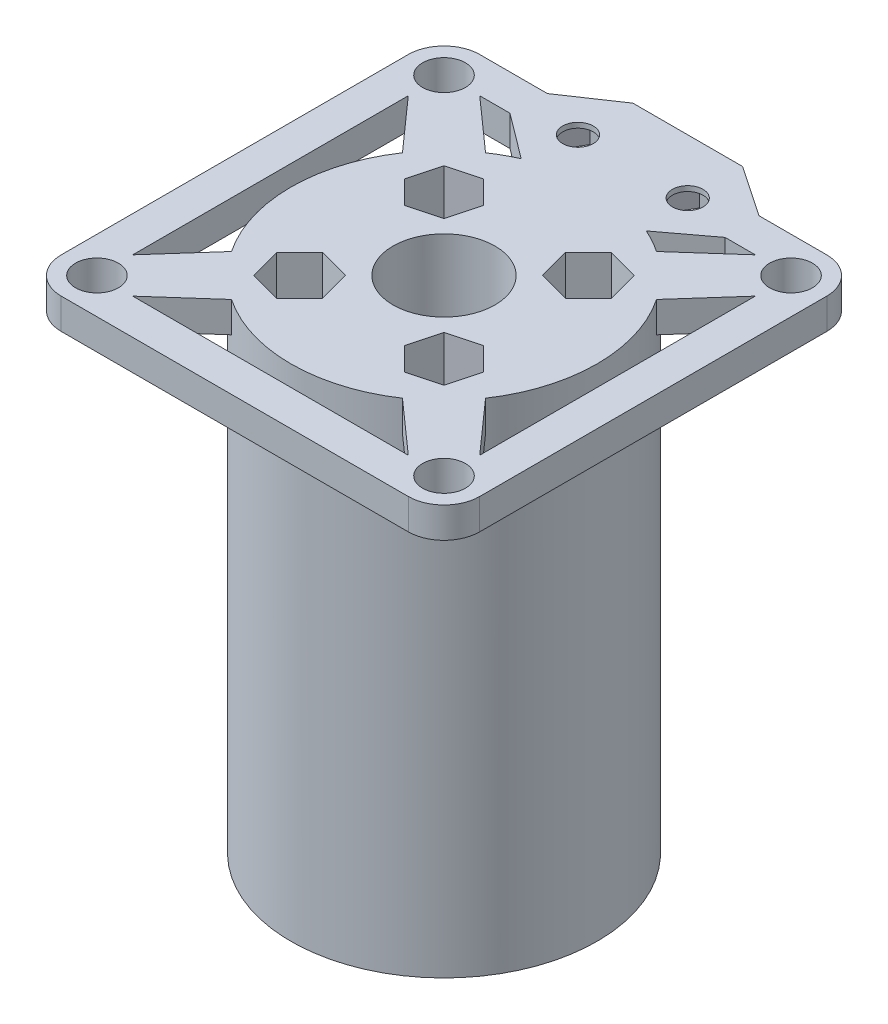
SolidWorks part; units mm, degrees
ref_plane "前视基准面" through (0, 0, 0) normal (0, 0, 1) x (1, 0, 0)
ref_plane "上视基准面" through (0, 0, 0) normal (0, 1, 0) x (1, 0, 0)
ref_plane "右视基准面" through (0, 0, 0) normal (1, 0, 0) x (0, 0, -1)
sketch "草图1" plane through (0, 0, 0) normal (0, 1, 0) x (1, 0, 0)
  circle A0 centre (-5.3729, -8.9317) radius 15
  circle A1 centre (-22.3729, 8.0683) radius 2.1
  circle A5 centre (-5.3729, -8.9317) radius 5
  circle A6 centre (-22.3729, 8.0683) radius 3.5
  dimension "D4" = 4.2
  dimension "D8" = 10
  dimension "D9" = 7
extrude "凸台-拉伸4" add sketch "草图1" along normal blind 3
sketch "草图5" plane through (0, 0, 0) normal (0, 1, 0) x (1, 0, 0)
  line L0 (-22.3729, 4.5683) -> (-10.3729, -8.9317)
  line L1 (-5.3729, -3.9317) -> (-18.8729, 8.0683)
  line L2 (-18.8729, 8.0683) -> (-22.3729, 4.5683)
  line L3 (-10.3729, -8.9317) -> (-10.3729, -3.9317)
  line L4 (-10.3729, -3.9317) -> (-5.3729, -3.9317)
  circle A0 centre (-22.3729, 8.0683) radius 3.5 construction
  circle A1 centre (-5.3729, -8.9317) radius 5 construction
extrude "凸台-拉伸5" add sketch "草图5" along normal blind 3
pattern_circular "阵列(圆周)2" count 4 over 360 about axis through (-5.3729, 0, 8.9317) along (0, 1, 0) of "凸台-拉伸5"
sketch "草图6" plane through (0, 3, 0) normal (0, 1, 0) x (1, 0, 0)
  circle A0 centre (11.6271, 8.0683) radius 2.1
  circle A1 centre (11.6271, 8.0683) radius 3.5
  dimension "D2" = 4.2
  dimension "D3" = 7
extrude "凸台-拉伸6" add sketch "草图6" against normal blind 3
pattern_circular "阵列(圆周)3" count 4 over 360 about axis through (-5.3729, 0, 8.9317) along (0, 1, 0) of "凸台-拉伸6"
sketch "草图7" plane through (0, 0, 0) normal (0, -1, 0) x (1, 0, 0)
  circle A0 centre (-5.3729, 8.9317) radius 15
  circle A1 centre (-5.3729, 8.9317) radius 5
extrude "凸台-拉伸7" add sketch "草图7" along normal blind 46
sketch "草图8" plane through (0, -46, 0) normal (0, -1, 0) x (1, 0, 0)
  line L4 (3.9435, 18.2482) -> (0.8763, 19.07)
  line L5 (0.8763, 19.07) -> (-1.3691, 16.8247)
  line L6 (-1.3691, 16.8247) -> (-0.5472, 13.7574)
  line L7 (-0.5472, 13.7574) -> (2.52, 12.9356)
  line L8 (2.52, 12.9356) -> (4.7654, 15.1809)
  line L9 (4.7654, 15.1809) -> (3.9435, 18.2482)
  circle A3 centre (1.6982, 16.0028) radius 2.75 construction
  dimension "D1" = 5.5
sketch "草图9" plane through (0, 3, 0) normal (0, 1, 0) x (1, 0, 0)
  line L0 (0.8763, -19.07) -> (-1.3691, -16.8247) construction
  line L1 (3.9435, -18.2482) -> (0.8763, -19.07) construction
  line L2 (4.7654, -15.1809) -> (3.9435, -18.2482) construction
  line L3 (2.52, -12.9356) -> (4.7654, -15.1809) construction
  line L4 (-0.5472, -13.7574) -> (2.52, -12.9356) construction
  line L5 (-1.3691, -16.8247) -> (-0.5472, -13.7574) construction
  line L6 (0.8763, -19.07) -> (-1.3691, -16.8247)
  line L7 (3.9435, -18.2482) -> (0.8763, -19.07)
  line L8 (4.7654, -15.1809) -> (3.9435, -18.2482)
  line L9 (2.52, -12.9356) -> (4.7654, -15.1809)
  line L10 (-0.5472, -13.7574) -> (2.52, -12.9356)
  line L11 (-1.3691, -16.8247) -> (-0.5472, -13.7574)
extrude "切除-拉伸1" cut sketch "草图9" against normal blind 46
pattern_circular "阵列(圆周)4" count 4 over 360 about axis through (-5.3729, 0, 8.9317) along (0, 1, 0) of "切除-拉伸1"
sketch "草图11" plane through (0, -43, 0) normal (0, 1, 0) x (1, 0, 0)
  circle A0 centre (1.6982, -1.8607) radius 1.5
  dimension "D1" = 3
extrude "切除-拉伸2" cut sketch "草图11" against normal blind 3
pattern_circular "阵列(圆周)5" count 4 over 360 about axis through (-5.3729, 0, 8.9317) along (0, 1, 0) of "切除-拉伸2"
sketch "草图12" plane through (0, 3, 0) normal (0, 1, 0) x (1, 0, 0)
  line L0 (15.1271, 8.0683) -> (15.1271, -25.9317)
  line L1 (15.1271, -25.9317) -> (11.6271, -22.4317)
  line L2 (11.6271, -22.4317) -> (11.6271, 4.5683)
  line L3 (11.6271, 4.5683) -> (15.1271, 8.0683)
  arc A0 (11.6271, 4.5683) -> (8.1271, 8.0683) centre (11.6271, 8.0683) ccw construction
  arc A1 (8.1271, -25.9317) -> (11.6271, -22.4317) centre (11.6271, -25.9317) ccw construction
extrude "凸台-拉伸8" add sketch "草图12" against normal blind 3
sketch "草图13" plane through (0, 3, 0) normal (0, 1, 0) x (1, 0, 0)
  line L0 (11.6271, 11.5683) -> (-22.3729, 11.5683)
  line L1 (-22.3729, 11.5683) -> (-18.8729, 8.0683)
  line L2 (-18.8729, 8.0683) -> (8.1271, 8.0683)
  line L3 (8.1271, 8.0683) -> (11.6271, 11.5683)
  arc A0 (15.1271, 8.0683) -> (8.1271, 8.0683) centre (11.6271, 8.0683) ccw construction
  arc A1 (-18.8729, 8.0683) -> (-22.3729, 4.5683) centre (-22.3729, 8.0683) ccw construction
extrude "凸台-拉伸9" add sketch "草图13" against normal blind 3
sketch "草图14" plane through (0, 3, 0) normal (0, 1, 0) x (1, 0, 0)
  line L0 (-25.8729, 8.0683) -> (-25.8729, -25.9317)
  line L1 (-25.8729, -25.9317) -> (-22.3729, -22.4317)
  line L2 (-22.3729, -22.4317) -> (-22.3729, 4.5683)
  line L3 (-22.3729, 4.5683) -> (-25.8729, 8.0683)
  arc A0 (-22.3729, 11.5683) -> (-22.3729, 4.5683) centre (-22.3729, 8.0683) ccw construction
  arc A1 (-22.3729, -22.4317) -> (-18.8729, -25.9317) centre (-22.3729, -25.9317) ccw construction
extrude "凸台-拉伸10" add sketch "草图14" against normal blind 3
sketch "草图15" plane through (0, 3, 0) normal (0, 1, 0) x (1, 0, 0)
  line L0 (-22.3729, -29.4317) -> (11.6271, -29.4317)
  line L1 (11.6271, -29.4317) -> (8.1271, -25.9317)
  line L2 (8.1271, -25.9317) -> (-18.8729, -25.9317)
  line L3 (-18.8729, -25.9317) -> (-22.3729, -29.4317)
  arc A0 (-25.8729, -25.9317) -> (-18.8729, -25.9317) centre (-22.3729, -25.9317) ccw construction
  arc A1 (8.1271, -25.9317) -> (15.1271, -25.9317) centre (11.6271, -25.9317) ccw construction
extrude "凸台-拉伸11" add sketch "草图15" against normal blind 3
sketch "草图16" plane through (0, 0, 0) normal (0, -1, 0) x (1, 0, 0)
  line L0 (-10.7479, -4.1933) -> (0.0021, -4.1933)
  line L1 (0.0021, -4.1933) -> (5.1636, -8.0683)
  line L2 (-18.8729, -8.0683) -> (8.1271, -8.0683) construction
  line L3 (4.9912, -11.5683) -> (0.0021, -14.9433)
  line L4 (11.6271, -11.5683) -> (-22.3729, -11.5683) construction
  line L5 (-7.5725, -9.5683) -> (-9.1602, -6.8183)
  line L6 (-9.1602, -6.8183) -> (-12.3356, -6.8183)
  line L7 (-12.3356, -6.8183) -> (-13.9233, -9.5683)
  line L8 (-13.9233, -9.5683) -> (-12.3356, -12.3183)
  line L9 (-12.3356, -12.3183) -> (-9.1602, -12.3183)
  line L10 (-9.1602, -12.3183) -> (-7.5725, -9.5683)
  line L11 (3.1775, -9.5683) -> (1.5898, -6.8183)
  line L12 (1.5898, -6.8183) -> (-1.5856, -6.8183)
  line L13 (-1.5856, -6.8183) -> (-3.1733, -9.5683)
  line L14 (-3.1733, -9.5683) -> (-1.5856, -12.3183)
  line L15 (-1.5856, -12.3183) -> (1.5898, -12.3183)
  line L16 (1.5898, -12.3183) -> (3.1775, -9.5683)
  line L17 (0.0021, -14.9433) -> (-10.7479, -14.9433)
  line L18 (-10.7479, -14.9433) -> (-15.7369, -11.5683)
  line L19 (-15.7369, -11.5683) -> (-15.9094, -8.0683)
  line L20 (-15.9094, -8.0683) -> (-10.7479, -4.1933)
  line L21 (4.9912, -11.5683) -> (5.1636, -8.0683)
  circle A0 centre (-10.7479, -9.5683) radius 2.75 construction
  circle A2 centre (0.0021, -9.5683) radius 2.75 construction
  dimension "D4" = 5.5
  dimension "D5" = 5.5
sketch "草图17" plane through (0, 0, 0) normal (0, -1, 0) x (1, 0, 0)
  line L1 (-7.5725, -9.5683) -> (-9.1602, -6.8183)
  line L2 (-9.1602, -6.8183) -> (-12.3356, -6.8183)
  line L3 (-12.3356, -6.8183) -> (-13.9233, -9.5683)
  line L4 (-13.9233, -9.5683) -> (-12.3356, -12.3183)
  line L5 (-12.3356, -12.3183) -> (-9.1602, -12.3183)
  line L6 (-9.1602, -12.3183) -> (-7.5725, -9.5683)
  line L7 (3.1775, -9.5683) -> (1.5898, -6.8183)
  line L8 (1.5898, -6.8183) -> (-1.5856, -6.8183)
  line L9 (-1.5856, -6.8183) -> (-3.1733, -9.5683)
  line L10 (-3.1733, -9.5683) -> (-1.5856, -12.3183)
  line L11 (-1.5856, -12.3183) -> (1.5898, -12.3183)
  line L12 (1.5898, -12.3183) -> (3.1775, -9.5683)
  circle A0 centre (-10.7479, -9.5683) radius 2.75 construction
  circle A1 centre (0.0021, -9.5683) radius 2.75 construction
extrude "凸台-拉伸13" add sketch "草图16" against normal blind 3
sketch "草图18" plane through (0, 0, 0) normal (0, -1, 0) x (1, 0, 0)
  line L1 (-7.5725, -9.5683) -> (-9.1602, -6.8183)
  line L2 (-9.1602, -6.8183) -> (-12.3356, -6.8183)
  line L3 (-12.3356, -6.8183) -> (-13.9233, -9.5683)
  line L4 (-13.9233, -9.5683) -> (-12.3356, -12.3183)
  line L5 (-12.3356, -12.3183) -> (-9.1602, -12.3183)
  line L6 (-9.1602, -12.3183) -> (-7.5725, -9.5683)
  line L7 (3.1775, -9.5683) -> (1.5898, -6.8183)
  line L8 (1.5898, -6.8183) -> (-1.5856, -6.8183)
  line L9 (-1.5856, -6.8183) -> (-3.1733, -9.5683)
  line L10 (-3.1733, -9.5683) -> (-1.5856, -12.3183)
  line L11 (-1.5856, -12.3183) -> (1.5898, -12.3183)
  line L12 (1.5898, -12.3183) -> (3.1775, -9.5683)
  circle A0 centre (-10.7479, -9.5683) radius 2.75 construction
  circle A1 centre (0.0021, -9.5683) radius 2.75 construction
extrude "凸台-拉伸14" add sketch "草图18" against normal blind 3
extrude "切除-拉伸3" cut sketch "草图17" against normal blind 2.5
sketch "草图19" plane through (0, 2.5, 0) normal (0, -1, 0) x (1, 0, 0)
  circle A0 centre (0.0021, -9.5683) radius 1.5
  dimension "D1" = 3
extrude "切除-拉伸4" cut sketch "草图19" against normal blind 2.5
sketch "草图20" plane through (0, 2.5, 0) normal (0, -1, 0) x (1, 0, 0)
  circle A0 centre (-10.7479, -9.5683) radius 1.5
  dimension "D1" = 3
extrude "切除-拉伸5" cut sketch "草图20" against normal blind 2.5
sketch "草图21" plane through (0, 0, 0) normal (0, 1, 0) x (1, 0, 0)
  circle A0 centre (59.6655, -8.9317) radius 15
  circle A1 centre (59.6655, -8.9317) radius 5
  dimension "D1" = 30
  dimension "D2" = 10
extrude "凸台-拉伸15" add sketch "草图21" along normal blind 3 separate body
sketch "草图22" plane through (0, 0, 0) normal (0, -1, 0) x (1, 0, 0)
  circle A0 centre (59.6655, 18.9317) radius 1.5
  dimension "D2" = 3
extrude "切除-拉伸6" cut sketch "草图22" against normal blind 3
pattern_circular "阵列(圆周)6" count 4 over 360 about axis through (59.6655, 0, 8.9317) along (0, 1, 0) of "切除-拉伸6"
extrude "凸台-拉伸16" add sketch "草图8" along normal blind 3
sketch "草图24" plane through (0, -49, 0) normal (0, -1, 0) x (1, 0, 0)
  line L1 (4.7654, 15.1809) -> (3.9435, 18.2482)
  line L2 (3.9435, 18.2482) -> (0.8763, 19.07)
  line L3 (0.8763, 19.07) -> (-1.3691, 16.8247)
  line L4 (-1.3691, 16.8247) -> (-0.5472, 13.7574)
  line L5 (-0.5472, 13.7574) -> (2.52, 12.9356)
  line L6 (2.52, 12.9356) -> (4.7654, 15.1809)
  circle A0 centre (1.6982, 16.0028) radius 2.75 construction
extrude "切除-拉伸7" cut sketch "草图24" against normal blind 3
sketch "草图25" plane through (0, 0, 0) normal (0, -1, 0) x (1, 0, 0)
  circle A0 centre (59.6655, 8.9317) radius 15
  circle A1 centre (59.6655, 8.9317) radius 5
extrude "凸台-拉伸17" add sketch "草图25" along normal blind 43
sketch "草图27" plane through (0, 3, 0) normal (0, 1, 0) x (1, 0, 0)
  circle A0 centre (59.6655, 1.0683) radius 1.5
  circle A1 centre (69.6655, -8.9317) radius 1.5
  circle A2 centre (59.6655, -18.9317) radius 1.5
  circle A3 centre (49.6655, -8.9317) radius 1.5
extrude "切除-拉伸8" cut sketch "草图27" against normal blind 46
sketch "草图28" plane through (0, -43, 0) normal (0, -1, 0) x (1, 0, 0)
  circle A0 centre (59.6655, 18.9317) radius 2.75
  circle A1 centre (49.6655, 8.9317) radius 2.75
  circle A2 centre (59.6655, -1.0683) radius 2.75
  circle A3 centre (69.6655, 8.9317) radius 2.75
  dimension "D1" = 5.5
  dimension "D2" = 5.5
  dimension "D3" = 5.5
  dimension "D4" = 5.5
extrude "切除-拉伸9" cut sketch "草图28" against normal blind 43
sketch "草图29" plane through (0, 3, 0) normal (0, 1, 0) x (1, 0, 0)
  circle A0 centre (66.7366, -1.8607) radius 1.5
  dimension "D2" = 3
extrude "切除-拉伸10" cut sketch "草图29" against normal blind 46
pattern_circular "阵列(圆周)7" count 4 over 360 about axis through (59.6655, 0, 8.9317) along (0, 1, 0) of "切除-拉伸10"
sketch "草图30" plane through (0, 3, 0) normal (0, 1, 0) x (1, 0, 0)
  line L2 (64.4912, -4.106) -> (67.5585, -4.9279)
  line L3 (67.5585, -4.9279) -> (69.8038, -2.6825)
  line L4 (69.8038, -2.6825) -> (68.982, 0.3847)
  line L5 (68.982, 0.3847) -> (65.9148, 1.2066)
  line L6 (65.9148, 1.2066) -> (63.6694, -1.0388)
  line L7 (63.6694, -1.0388) -> (64.4912, -4.106)
  circle A0 centre (66.7366, -1.8607) radius 2.75 construction
  dimension "D1" = 5.5
extrude "切除-拉伸11" cut sketch "草图30" against normal blind 43
pattern_circular "阵列(圆周)8" count 4 over 360 about axis through (59.6655, 0, 8.9317) along (0, 1, 0) of "切除-拉伸11"
sketch "草图31" plane through (0, 3, 0) normal (0, 1, 0) x (1, 0, 0)
  circle A0 centre (59.6655, -8.9317) radius 29.741
extrude "切除-拉伸12" cut sketch "草图31" against normal blind 100
